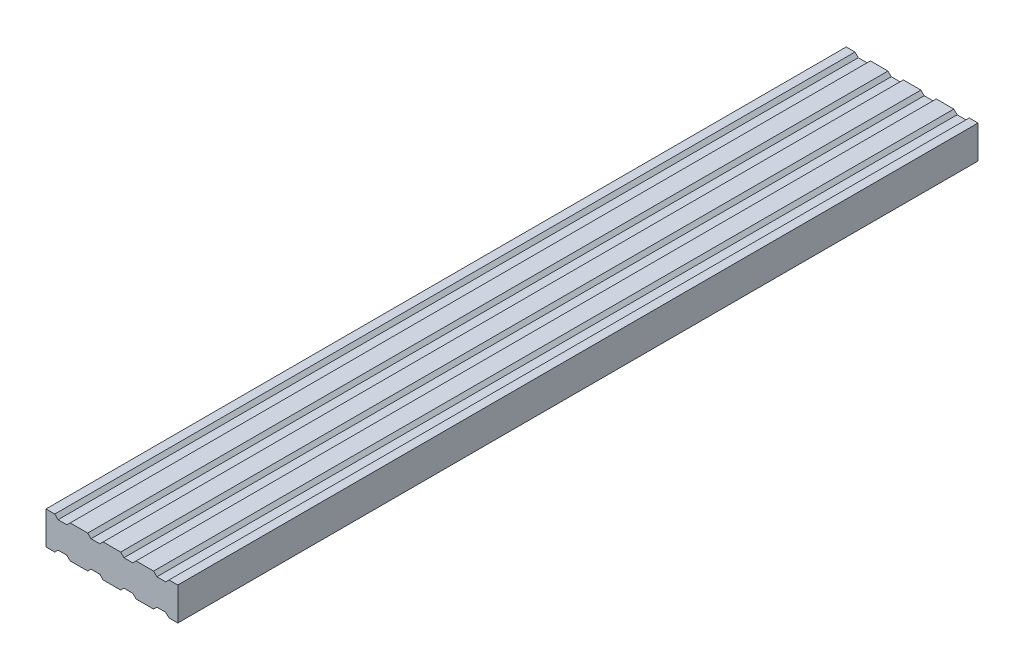
SolidWorks part; units mm, degrees
ref_plane "Front Plane" through (0, 0, 0) normal (0, 0, 1) x (1, 0, 0)
ref_plane "Top Plane" through (0, 0, 0) normal (0, 1, 0) x (1, 0, 0)
ref_plane "Right Plane" through (0, 0, 0) normal (1, 0, 0) x (0, 0, -1)
sketch "Sketch1" plane through (0, 0, 0) normal (0, 0, 1) x (1, 0, 0)
  line L0 (34.6716, -10) -> (40, -10)
  line L1 (40, -10) -> (40, 10)
  line L2 (40, 10) -> (34.6716, 10)
  line L3 (34.6716, 10) -> (32.6716, 8)
  line L4 (32.6716, 8) -> (27.3284, 8)
  line L5 (27.3284, 8) -> (25.3284, 10)
  line L6 (25.3284, 10) -> (14.6716, 10)
  line L7 (14.6716, 10) -> (12.6716, 8)
  line L8 (12.6716, 8) -> (7.3284, 8)
  line L9 (7.3284, 8) -> (5.3284, 10)
  line L10 (5.3284, 10) -> (-5.3284, 10)
  line L11 (-5.3284, 10) -> (-7.3284, 8)
  line L12 (-7.3284, 8) -> (-12.6716, 8)
  line L13 (-12.6716, 8) -> (-14.6716, 10)
  line L14 (-14.6716, 10) -> (-25.3284, 10)
  line L15 (-25.3284, 10) -> (-27.3284, 8)
  line L16 (-27.3284, 8) -> (-32.6716, 8)
  line L17 (-32.6716, 8) -> (-34.6716, 10)
  line L18 (-34.6716, 10) -> (-40, 10)
  line L19 (-40, 10) -> (-40, -10)
  line L20 (-40, -10) -> (-34.6716, -10)
  line L21 (-34.6716, -10) -> (-32.6716, -8)
  line L22 (-32.6716, -8) -> (-27.3284, -8)
  line L23 (-27.3284, -8) -> (-25.3284, -10)
  line L24 (-25.3284, -10) -> (-14.6716, -10)
  line L25 (-14.6716, -10) -> (-12.6716, -8)
  line L26 (-12.6716, -8) -> (-7.3284, -8)
  line L27 (-7.3284, -8) -> (-5.3284, -10)
  line L28 (-5.3284, -10) -> (5.3284, -10)
  line L29 (5.3284, -10) -> (7.3284, -8)
  line L30 (7.3284, -8) -> (12.6716, -8)
  line L31 (12.6716, -8) -> (14.6716, -10)
  line L32 (14.6716, -10) -> (25.3284, -10)
  line L33 (25.3284, -10) -> (27.3284, -8)
  line L34 (27.3284, -8) -> (32.6716, -8)
  line L35 (32.6716, -8) -> (34.6716, -10)
  dimension "D1" = 5.3284
  dimension "D2" = 7.3284
  dimension "D3" = 12.6716
extrude "Boss-Extrude1" add sketch "Sketch1" along normal blind 485.87
